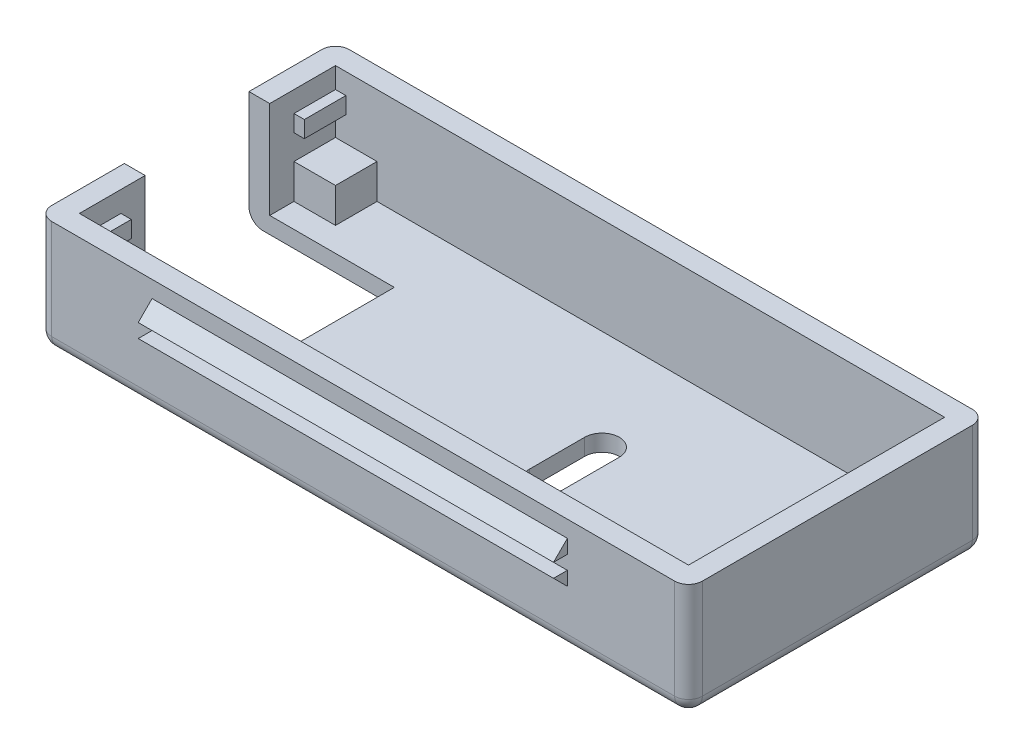
SolidWorks part; units mm, degrees
ref_plane "Front Plane" through (0, 0, 0) normal (0, 0, 1) x (1, 0, 0)
ref_plane "Top Plane" through (0, 0, 0) normal (0, 1, 0) x (1, 0, 0)
ref_plane "Right Plane" through (0, 0, 0) normal (1, 0, 0) x (0, 0, -1)
sketch "Sketch1" plane through (0, 0, 0) normal (0, 1, 0) x (1, 0, 0)
  line L1 (0, 0) -> (44, 0)
  line L2 (0, 0) -> (0, 18.5)
  line L3 (0, 18.5) -> (44, 18.5)
  line L4 (44, 0) -> (44, 18.5)
  dimension "D1" = 44
  dimension "D2" = 18.5
extrude "Extrude-Thin1" add sketch "Sketch1" along normal blind 7 thin
sketch "Sketch2" plane through (0, 0, 0) normal (0, -1, 0) x (1, 0, 0)
  line L1 (-1.5, -20) -> (45.5, -20)
  line L2 (-1.5, -20) -> (-1.5, 1.5)
  line L3 (-1.5, 1.5) -> (45.5, 1.5)
  line L4 (45.5, -20) -> (45.5, 1.5)
extrude "Boss-Extrude1" add sketch "Sketch2" along normal blind 1.2
sketch "Sketch3" plane through (0, -1.2, 0) normal (0, -1, 0) x (1, 0, 0)
  line L0 (-1.5, -9.25) -> (72.4552, -9.25) construction
  line L1 (-1.5, 1.5) -> (-1.5, -20) construction
  line L3 (-12, -13.75) -> (9, -13.75)
  line L4 (-12, -13.75) -> (-12, -4.75)
  line L5 (-12, -4.75) -> (9, -4.75)
  line L6 (9, -13.75) -> (9, -4.75)
  line L7 (-12, -13.75) -> (9, -4.75) construction
  line L8 (-12, -4.75) -> (9, -13.75) construction
  dimension "D1" = 10.5
  dimension "D2" = 9
extrude "Cut-Extrude1" cut sketch "Sketch3" against normal through all
sketch "Sketch4" plane through (0, -1.2, 0) normal (0, -1, 0) x (1, 0, 0)
  line L0 (9, -9.25) -> (63.1236, -9.25) construction
  line L1 (9, -13.75) -> (9, -4.75) construction
  line L2 (26.5, -11.25) -> (26.5, -7.25) construction
  line L3 (25.25, -11.25) -> (25.25, -7.25)
  line L4 (27.75, -11.25) -> (27.75, -7.25)
  line L5 (34.5, -18.5) -> (34.5, 0) construction
  line L6 (44, -18.5) -> (0, -18.5) construction
  line L7 (0, 0) -> (44, 0) construction
  line L8 (42.5, -11.25) -> (42.5, -7.25) construction
  line L9 (43.75, -11.25) -> (43.75, -7.25)
  line L10 (41.25, -11.25) -> (41.25, -7.25)
  arc A0 (25.25, -11.25) -> (27.75, -11.25) centre (26.5, -11.25) ccw
  arc A1 (27.75, -7.25) -> (25.25, -7.25) centre (26.5, -7.25) ccw
  arc A2 (43.75, -11.25) -> (41.25, -11.25) centre (42.5, -11.25) cw
  arc A3 (41.25, -7.25) -> (43.75, -7.25) centre (42.5, -7.25) cw
  point P6 (26.5, -9.25)
  point P19 (42.5, -9.25)
  dimension "D1" = 17.5
  dimension "D2" = 2.5
  dimension "D3" = 4
  dimension "D4" = 8
extrude "Cut-Extrude2" cut sketch "Sketch4" against normal through all
ref_plane "Plane1" through (0, 5.5, 0) normal (0, -1, 0) x (-1, 0, 0)
sketch "Sketch5" plane through (0, 5.5, 0) normal (0, -1, 0) x (-1, 0, 0)
  line L1 (0, 0) -> (-44, 0)
  line L2 (0, 0) -> (0, 18.5)
  line L3 (0, 18.5) -> (-44, 18.5)
  line L4 (-44, 0) -> (-44, 18.5)
extrude "Boss-Extrude2" add sketch "Sketch5" along normal blind 1.2
sketch "Sketch6" plane through (0, 4.3, 0) normal (0, -1, 0) x (-1, 0, 0)
  line L0 (-22, 18.5) -> (-22, 0) construction
  line L1 (-44, 18.5) -> (0, 18.5) construction
  line L2 (0, 0) -> (-44, 0) construction
  line L3 (-22, 9.25) -> (0, 9.25) construction
  line L4 (0, 4.75) -> (0, 13.75) construction
  line L5 (-44, 0) -> (-44, 18.5) construction
  line L6 (0, 3) -> (-44, 3)
  line L7 (0, 3) -> (0, 15.5)
  line L8 (0, 15.5) -> (-44, 15.5)
  line L9 (-44, 3) -> (-44, 15.5)
  line L10 (0, 3) -> (-44, 15.5) construction
  line L11 (0, 15.5) -> (-44, 3) construction
  dimension "D1" = 3
extrude "Cut-Extrude3" cut sketch "Sketch6" against normal blind 1.2
ref_plane "Plane2" through (0, 5.5, 0) normal (0, 1, 0) x (1, 0, 0)
sketch "Sketch9" plane through (0, 5.5, 0) normal (0, 1, 0) x (1, 0, 0)
  line L0 (22, 18.5) -> (22, 0) construction
  line L1 (0, 18.5) -> (44, 18.5) construction
  line L2 (0, 0) -> (44, 0) construction
  line L3 (44, 18.5) -> (0, 18.5) construction
  line L4 (0.75, 0) -> (43.25, 0)
  line L5 (0.75, 0) -> (0.75, 18.5)
  line L6 (0.75, 18.5) -> (43.25, 18.5)
  line L7 (43.25, 0) -> (43.25, 18.5)
  line L8 (0.75, 0) -> (43.25, 18.5) construction
  line L9 (0.75, 18.5) -> (43.25, 0) construction
  line L10 (44, 0) -> (44, 18.5) construction
  point P6 (22, 9.25)
  dimension "D1" = 0.75
extrude "Cut-Extrude4" cut sketch "Sketch9" against normal blind 3
ref_plane "Plane3" through (21.75, 0, 0) normal (-1, 0, 0) x (0, 0, 1)
sketch "Sketch10" plane through (21.75, 0, 0) normal (-1, 0, 0) x (0, 0, 1)
  line L0 (-20, 2.8) -> (1.5, 2.8) construction
  line L1 (-20, 7) -> (-20, -1.2) construction
  line L2 (1.5, 7) -> (1.5, -1.2) construction
  line L3 (-13.75, -1.2) -> (-20, -1.2) construction
  line L4 (-9.25, 10.7069) -> (-9.25, -4.1069) construction
  line L9 (-20, 2.8) -> (-21, 3.8)
  line L10 (-21, 3.8) -> (-20, 3.8)
  line L11 (-20, 3.8) -> (-20, 2.8)
  line L12 (2.5, 3.8) -> (1.5, 3.8)
  line L13 (1.5, 2.8) -> (2.5, 3.8)
  line L14 (1.5, 3.8) -> (1.5, 2.8)
  line L15 (4.0441, 4.3) -> (-22.5441, 4.3) construction
  line L16 (1.5, 5.8) -> (2.5, 4.8)
  line L17 (1.5, 4.8) -> (1.5, 5.8)
  line L18 (2.5, 4.8) -> (1.5, 4.8)
  line L19 (-21, 4.8) -> (-20, 4.8)
  line L20 (-20, 5.8) -> (-21, 4.8)
  line L21 (-20, 4.8) -> (-20, 5.8)
  point P17 (-9.25, 4.3)
  dimension "D2" = 1
  dimension "D4" = 1.5
  dimension "D1" = 4
  dimension "D3" = 1
extrude "Boss-Extrude3" add sketch "Sketch10" along normal blind 15 and the other way blind 15
sketch "Sketch13" plane through (0, 0, 0) normal (0, 1, 0) x (1, 0, 0)
  line L0 (22, 18.5) -> (22, 0) construction
  line L1 (44, 18.5) -> (0, 18.5) construction
  line L2 (0, 0) -> (44, 0) construction
  line L3 (0, 0) -> (3, 0)
  line L4 (44, 18.5) -> (41, 18.5)
  line L5 (44, 18.5) -> (44, 15.5)
  line L6 (44, 15.5) -> (41, 15.5)
  line L7 (41, 18.5) -> (41, 15.5)
  line L8 (44, 0) -> (41, 0)
  line L9 (44, 0) -> (44, 3)
  line L10 (44, 3) -> (41, 3)
  line L11 (41, 0) -> (41, 3)
  line L12 (0, 0) -> (0, 3)
  line L13 (0, 3) -> (3, 3)
  line L14 (3, 0) -> (3, 3)
  line L15 (0, 18.5) -> (3, 18.5)
  line L16 (0, 18.5) -> (0, 15.5)
  line L17 (0, 15.5) -> (3, 15.5)
  line L18 (3, 18.5) -> (3, 15.5)
  dimension "D1" = 3
  dimension "D2" = 3
  dimension "D3" = 3
  dimension "D4" = 3
extrude "Boss-Extrude4" add sketch "Sketch13" along normal blind 2.5
fillet "Fillet1" radius 1 4 edges at (-1.5, 2.9, -20) (45.5, 2.9, -20) (45.5, 2.9, 1.5) (-1.5, 2.9, 1.5)
fillet "Fillet2" radius 1 9 edges at (-1.2071, -1.2, 1.2071) (45.2071, -1.2, 1.2071) (45.2071, -1.2, -19.7071) (-1.2071, -1.2, -19.7071) (-1.5, -1.2, -2.125) (22, -1.2, 1.5) (45.5, -1.2, -9.25) (22, -1.2, -20) (-1.5, -1.2, -16.375)
